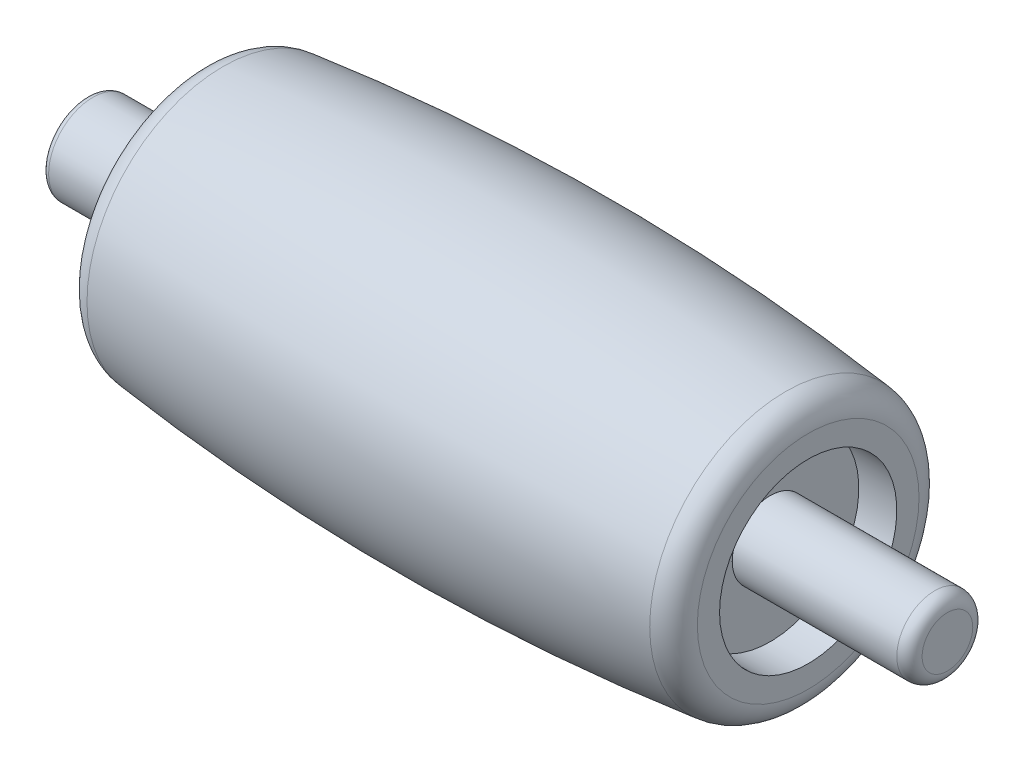
SolidWorks part; units mm, degrees
ref_plane "Front Plane" through (0, 0, 0) normal (0, 0, 1) x (1, 0, 0)
ref_plane "Top Plane" through (0, 0, 0) normal (0, 1, 0) x (1, 0, 0)
ref_plane "Right Plane" through (0, 0, 0) normal (1, 0, 0) x (0, 0, -1)
sketch "Sketch1" plane through (0, 0, 0) normal (0, 0, 1) x (1, 0, 0)
  line L0 (0, 0) -> (0, 6) construction
  line L1 (0, 0) -> (5.3568, 0) construction
  line L2 (-10.5, 1.5) -> (10.5, 1.5)
  line L3 (10.5, 1.5) -> (10.5, 3.5)
  line L4 (10.5, 3.5) -> (12, 3.5)
  line L5 (12, 3.5) -> (12, 4.3775)
  line L6 (-12, 3.5) -> (-12, 4.3775)
  line L7 (-10.5, 3.5) -> (-12, 3.5)
  line L8 (-10.5, 1.5) -> (-10.5, 3.5)
  arc A0 (-11.1128, 5.3711) -> (11.1128, 5.3711) centre (0, -92.5) cw
  arc A1 (12, 4.3775) -> (11.1128, 5.3711) centre (11, 4.3775) ccw
  arc A2 (-12, 4.3775) -> (-11.1128, 5.3711) centre (-11, 4.3775) cw
  point P13 (0, 1.5)
  point P16 (12, 5.2663)
  point P19 (-12, 5.2663)
  dimension "D6" = 1
  dimension "D1" = 1.5
  dimension "D2" = 3.5
  dimension "D3" = 1.5
  dimension "D4" = 12
  dimension "D5" = 6
revolve "Revolve2" add sketch "Sketch1" angle 360 about L1
sketch "Sketch2" plane through (10.5, 0, 0) normal (1, 0, 0) x (0, 0, -1)
  circle A0 centre (0, 0) radius 1.5 construction
  circle A1 centre (0, 0) radius 1.5
extrude "Boss-Extrude1" add sketch "Sketch2" along normal blind 7 separate body
sketch "Sketch3" plane through (-10.5, 0, 0) normal (-1, 0, 0) x (0, 0, 1)
  circle A2 centre (0, 0) radius 1.75
  dimension "D1" = 3.5
extrude "Boss-Extrude2" add sketch "Sketch3" along normal blind 6 separate body
fillet "Fillet1" radius 0.5 1 edges at (17.5, 0, -1.5)
fillet "Fillet2" radius 0.25 1 edges at (-16.5, 0, 1.75)
